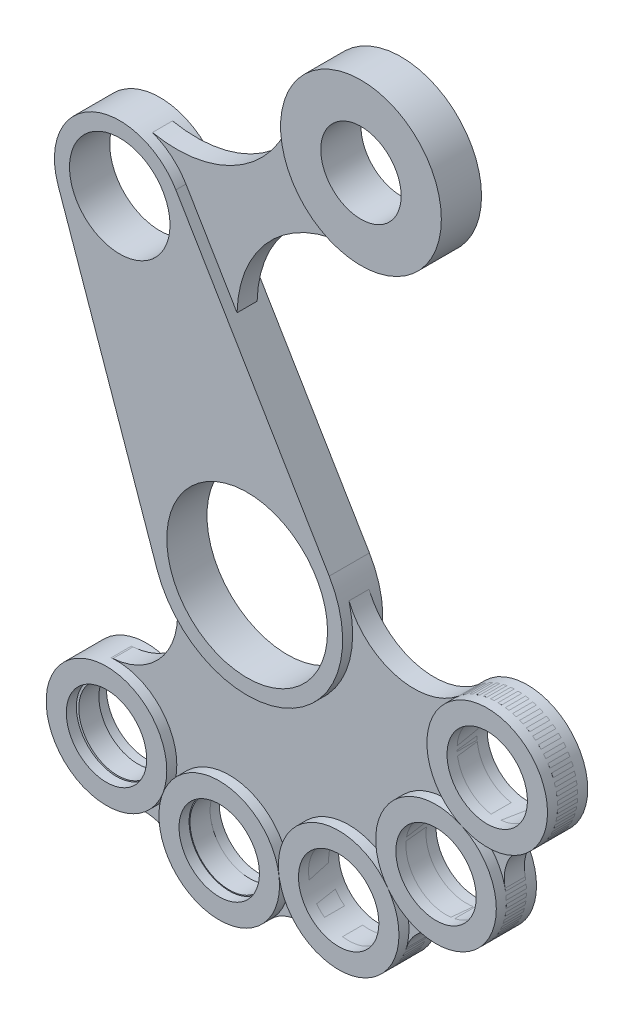
SolidWorks part; units mm, degrees
material "1345 Alloy"
ref_plane "Front Plane" through (0, 0, 0) normal (0, 0, 1) x (1, 0, 0)
ref_plane "Top Plane" through (0, 0, 0) normal (0, 1, 0) x (1, 0, 0)
ref_plane "Right Plane" through (0, 0, 0) normal (1, 0, 0) x (0, 0, -1)
sketch "Sketch1" plane through (0, 0, 0) normal (0, 0, 1) x (1, 0, 0)
  line L0 (0, 0) -> (317.6471, 0) construction
  line L1 (0, -165.0735) -> (0, 152.5735) construction
  line L2 (-94.0711, 125.23) -> (-44.8417, -15.6676)
  line L3 (-35.4557, 152.5609) -> (40.8271, 24.2775)
  circle A0 centre (-63.39, 135.95) radius 25
  circle A1 centre (0, 0) radius 40
  arc A2 (-35.4557, 152.5609) -> (-94.0711, 125.23) centre (-63.39, 135.95) ccw
  arc A3 (-44.8417, -15.6676) -> (40.8271, 24.2775) centre (0, 0) ccw
  dimension "D1" = 50
  dimension "D2" = 80
  dimension "D5" = 65
  dimension "D6" = 95
  dimension "D3" = 63.39
  dimension "D4" = 135.95
extrude "Boss-Extrude1" add sketch "Sketch1" along normal mid plane 20
sketch "Sketch2" plane through (0, 0, 0) normal (0, 0, 1) x (1, 0, 0)
  line L0 (-63.39, 135.95) -> (9.0466, 135.95) construction
  line L1 (-63.39, 135.95) -> (-63.39, 216.5423) construction
  line L3 (0, 0) -> (-70, -100) construction
  line L4 (-70, -100) -> (-107.2131, -153.1616) construction
  line L5 (-13.8973, -121.2719) -> (-67.5174, -197.8719) construction
  line L6 (45.5279, -112.987) -> (0, 0) construction
  line L7 (0, 0) -> (-13.8973, -121.2719) construction
  circle A0 centre (56.61, 205.95) radius 40
  circle A1 centre (56.61, 205.95) radius 20
  arc A2 (-70, -100) -> (119.8693, 23.0511) centre (0, 0) ccw construction
  circle A3 centre (-70, -100) radius 20
  circle A4 centre (-70, -100) radius 30
  circle A5 centre (-13.8973, -121.2719) radius 30
  circle A6 centre (-13.8973, -121.2719) radius 20
  circle A7 centre (93.9613, -77.5723) radius 30
  circle A8 centre (93.9613, -77.5723) radius 20
  circle A9 centre (45.5279, -112.987) radius 30
  circle A10 centre (45.5279, -112.987) radius 20
  circle A13 centre (119.4361, -23.2489) radius 30
  circle A14 centre (119.4361, -23.2489) radius 20
  circle A15 centre (116.1772, 36.6626) radius 30 [skipped]
  circle A16 centre (116.1772, 36.6626) radius 20 [skipped]
  point P17 (119.4361, 23.0511)
  point P33 (-0.2613, 0.0294)
  dimension "D1" = 80
  dimension "D2" = 40
  dimension "D5" = 40
  dimension "D6" = 60
  dimension "D9" = 60
  dimension "D10" = 40
  dimension "D3" = 70
  dimension "D4" = 120
  dimension "D7" = 100
  dimension "D8" = 70
  dimension "D11" = 3
extrude "Boss-Extrude2" add sketch "Sketch2" along normal mid plane 20 separate body contours A0 A1 | A13 A14 | A7 A8 | A9 A10 | A5 A6 | A4 A3
sketch "Sketch3" plane through (0, 0, 0) normal (0, 0, 1) x (1, 0, 0)
  line L0 (40.8271, 24.2775) -> (-35.4557, 152.5609) construction
  line L1 (0, 0) -> (53.3713, -131.3849) construction
  line L2 (-10.0352, 109.8118) -> (-35.4557, 152.5609)
  arc A0 (49.4549, 166.5952) -> (-10.0352, 109.8118) centre (48.1015, 108.4584) ccw
  circle A1 centre (56.61, 205.95) radius 40 construction
  arc A2 (-52.1465, 166.4432) -> (16.61, 205.95) centre (-40.2037, 225.2426) ccw
  arc A3 (-35.4557, 152.5609) -> (-94.0711, 125.23) centre (-63.39, 135.95) ccw construction
  arc A4 (43.8616, 19.1745) -> (100.3171, -0.1304) centre (78.0116, 26.8411) ccw
  circle A5 centre (119.4361, -23.2489) radius 30 construction
  circle A6 centre (45.5279, -112.987) radius 20 construction
  circle A7 centre (-70, -100) radius 30 construction
  arc A8 (-61.6779, -128.8226) -> (-39.2369, -137.3314) centre (-56.1299, -148.0377) cw
  circle A9 centre (-13.8973, -121.2719) radius 30 construction
  arc A10 (7.2442, -142.5565) -> (31.0143, -139.2426) centre (21.3385, -156.7463) cw
  circle A11 centre (45.5279, -112.987) radius 30 construction
  arc A12 (74.2238, -121.736) -> (94.1451, -107.5842) centre (93.3544, -127.5686) cw
  arc A13 (123.3332, -71.4652) -> (133.5231, -49.7358) centre (142.9144, -67.3938) cw
  circle A14 centre (93.9613, -77.5723) radius 30 construction
  arc A15 (-44.8417, -15.6676) -> (40.8271, 24.2775) centre (0, 0) ccw construction
  arc A16 (-45.808, -15.3086) -> (-71.8079, -70.0511) centre (-74.6302, -35.1651) cw
  arc A17 (-35.4557, 152.5609) -> (-52.1465, 166.4432) centre (-63.39, 135.95) ccw
  arc A19 (-39.2369, -137.3314) -> (7.2442, -142.5565) centre (-13.8973, -121.2719) ccw
  arc A21 (93.5972, -107.5701) -> (123.3332, -71.4652) centre (93.9613, -77.5723) ccw
  arc A22 (133.5231, -49.7358) -> (100.3171, -0.1304) centre (119.4361, -23.2489) ccw
  arc A23 (16.61, 205.95) -> (49.4549, 166.5952) centre (56.61, 205.95) ccw
  arc A24 (31.0143, -139.2426) -> (74.2238, -121.736) centre (45.5279, -112.987) ccw
  arc A26 (-71.8079, -70.0511) -> (-61.6779, -128.8226) centre (-69.3936, -99.8938) ccw
  arc A27 (-45.808, -15.3086) -> (-71.8079, -70.0511) centre (-74.6302, -35.1651) cw
  arc A28 (-71.8079, -70.0511) -> (-61.6779, -128.8226) centre (-69.3936, -99.8938) ccw
  arc A29 (-61.6779, -128.8226) -> (-39.2369, -137.3314) centre (-56.1299, -148.0377) cw
  arc A30 (-39.2369, -137.3314) -> (7.2442, -142.5565) centre (-13.8973, -121.2719) ccw
  arc A31 (7.2442, -142.5565) -> (31.0143, -139.2426) centre (21.3385, -156.7463) cw
  arc A32 (31.0143, -139.2426) -> (74.2238, -121.736) centre (45.5279, -112.987) ccw
  arc A33 (74.2238, -121.736) -> (94.1451, -107.5842) centre (93.3544, -127.5686) cw
  arc A34 (93.5972, -107.5701) -> (123.3332, -71.4652) centre (93.9613, -77.5723) ccw
  arc A35 (123.3332, -71.4652) -> (133.5231, -49.7358) centre (142.9144, -67.3938) cw
  arc A36 (133.5231, -49.7358) -> (100.3171, -0.1304) centre (119.4361, -23.2489) ccw
  arc A37 (100.3171, -0.1304) -> (43.8616, 19.1745) centre (78.0116, 26.8411) cw
  arc A38 (43.8616, 19.1745) -> (-45.808, -15.3086) centre (-0.9732, 1.933) cw
  circle A39 centre (-69.3936, -99.8938) radius 19.3844
  circle A40 centre (-13.8973, -121.2719) radius 19.5432
  circle A41 centre (45.5279, -112.987) radius 20
  circle A42 centre (93.9613, -77.5723) radius 20
  circle A43 centre (119.4361, -23.2489) radius 20
  dimension "D1" = 60
  dimension "D2" = 35
  dimension "D4" = 20
extrude "Boss-Extrude3" add sketch "Sketch3" along normal mid plane 10
